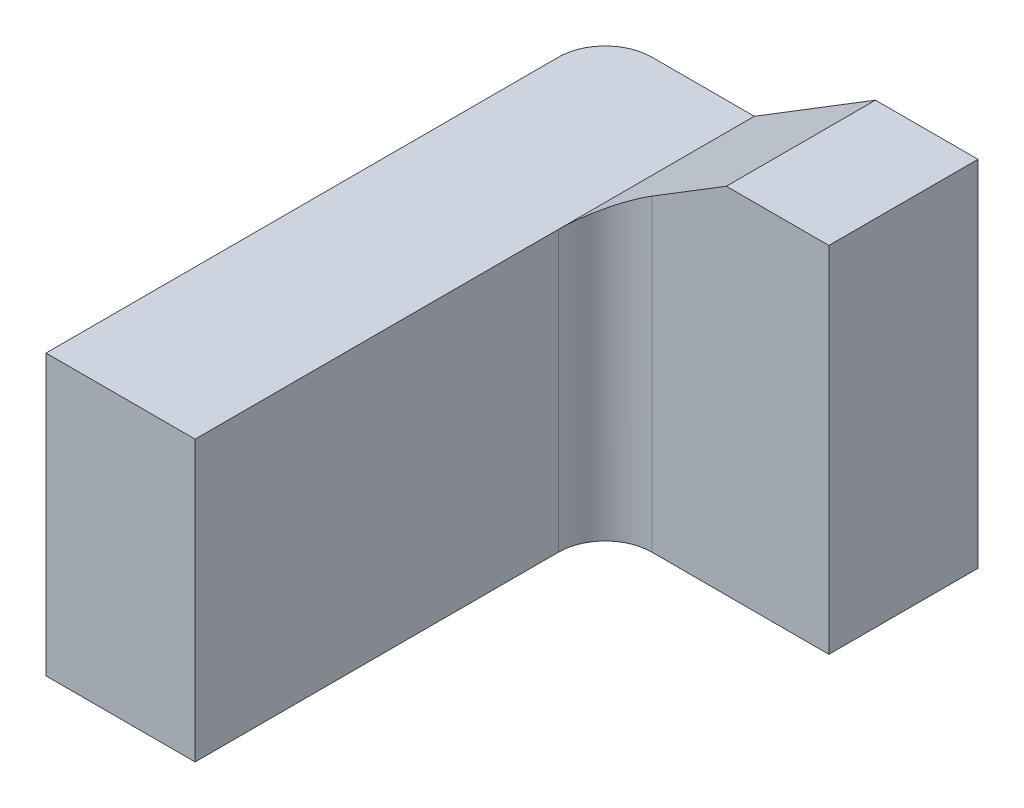
SolidWorks part; units mm, degrees
ref_plane "前视基准面" through (0, 0, 0) normal (0, 0, 1) x (1, 0, 0)
ref_plane "上视基准面" through (0, 0, 0) normal (0, 1, 0) x (1, 0, 0)
ref_plane "右视基准面" through (0, 0, 0) normal (1, 0, 0) x (0, 0, -1)
sketch "草图1" plane through (0, 0, 0) normal (0, 0, 1) x (1, 0, 0)
  line L0 (0, 0) -> (0, 0.3)
  line L1 (0, 0) -> (0.4, 0)
  line L2 (0.4, 0) -> (0.4, 0.38)
  line L3 (0.4, 0.38) -> (0.29, 0.38)
  line L4 (0, 0.3) -> (0.16, 0.3)
  line L5 (0.16, 0.3) -> (0.29, 0.38)
  dimension "D1" = 0.38
  dimension "D2" = 0.3
  dimension "D3" = 0.4
  dimension "D4" = 0.11
  dimension "D5" = 0.16
extrude "凸台-拉伸1" add sketch "草图1" along normal blind 0.16 contours L4 L5 L3 L2 L1 L0
sketch "草图2" plane through (0, 0, 0.16) normal (0, 0, 1) x (1, 0, 0)
  line L0 (0.16, 0.3) -> (0.16, 0) construction
  line L1 (0, 0) -> (0.4, 0) construction
  line L3 (0.16, 0) -> (0, 0)
  line L4 (0.16, 0) -> (0.16, 0.3)
  line L5 (0.16, 0.3) -> (0, 0.3)
  line L6 (0, 0) -> (0, 0.3)
extrude "凸台-拉伸2" add sketch "草图2" along normal blind 0.44
fillet "圆角1" radius 0.05 2 edges at (0, 0.15, 0) (0.16, 0.15, 0.16)
